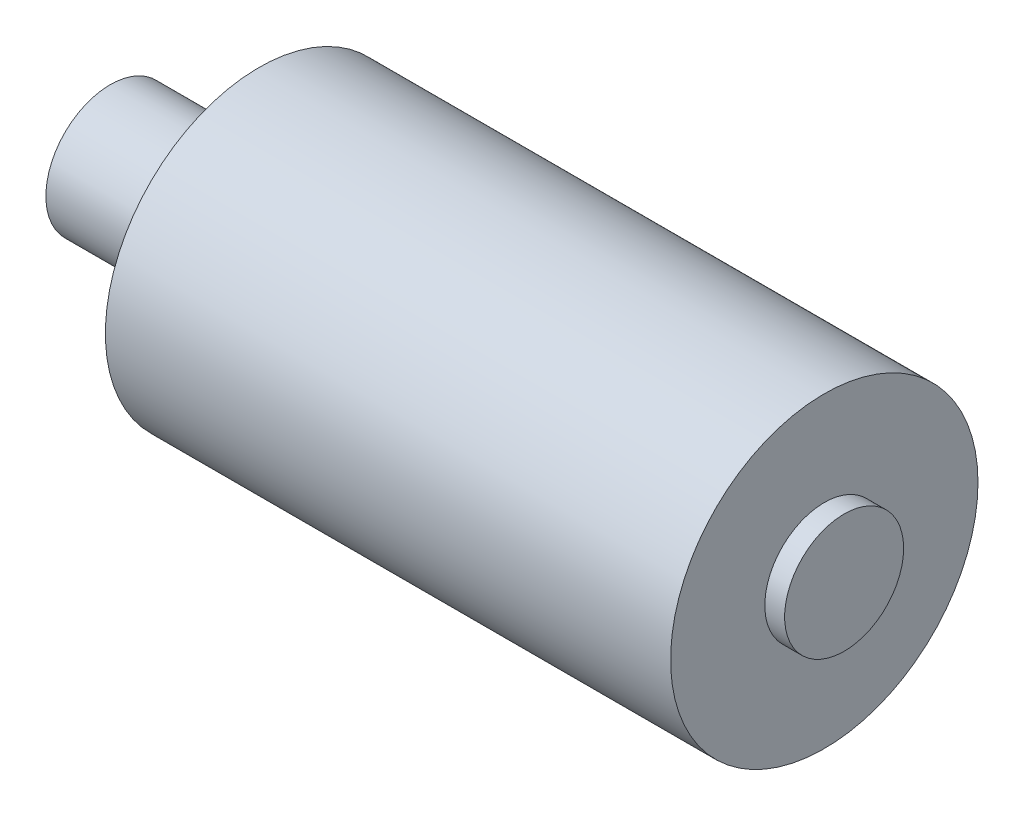
SolidWorks part; units mm, degrees
ref_plane "前视基准面" through (0, 0, 0) normal (0, 0, 1) x (1, 0, 0)
ref_plane "上视基准面" through (0, 0, 0) normal (0, 1, 0) x (1, 0, 0)
ref_plane "右视基准面" through (0, 0, 0) normal (1, 0, 0) x (0, 0, -1)
sketch "草图1" plane through (0, 0, 0) normal (1, 0, 0) x (0, 0, -1)
  circle A0 centre (0, 0) radius 15.5
  dimension "D1" = 31
extrude "凸台-拉伸1" add sketch "草图1" along normal blind 57
sketch "草图2" plane through (0, 0, 0) normal (1, 0, 0) x (0, 0, -1)
  circle A0 centre (0, 0) radius 6.5
  dimension "D1" = 13
extrude "凸台-拉伸2" add sketch "草图2" against normal blind 15
ref_plane "基准面1" through (57, 0, 0) normal (1, 0, 0) x (0, 0, -1)
sketch "草图3" plane through (57, 0, 0) normal (1, 0, 0) x (0, 0, -1)
  circle A0 centre (0, 0) radius 6
  dimension "D1" = 12
extrude "凸台-拉伸3" add sketch "草图3" along normal blind 2
